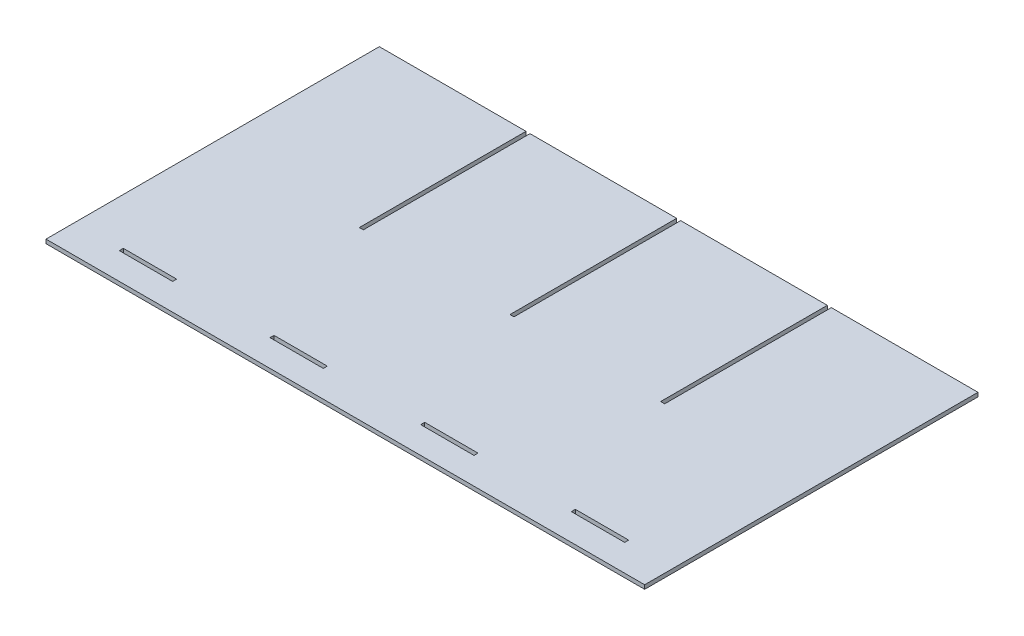
SolidWorks part; units mm, degrees
ref_plane "Front Plane" through (0, 0, 0) normal (0, 0, 1) x (1, 0, 0)
ref_plane "Top Plane" through (0, 0, 0) normal (0, 1, 0) x (1, 0, 0)
ref_plane "Right Plane" through (0, 0, 0) normal (1, 0, 0) x (0, 0, -1)
sketch "Sketch1" plane through (0, 0, 0) normal (0, 1, 0) x (1, 0, 0)
  line L0 (-162.3685, 89.9451) -> (-52.3685, 89.9451)
  line L1 (-52.3685, 89.9451) -> (-52.3685, -35.0549)
  line L2 (-49.3685, -35.0549) -> (-49.3685, 89.9451)
  line L3 (-49.3685, 89.9451) -> (60.6315, 89.9451)
  line L4 (60.6315, 89.9451) -> (60.6315, -35.0549)
  line L5 (60.6315, -35.0549) -> (63.6315, -35.0549)
  line L6 (63.6315, -35.0549) -> (63.6315, 89.9451)
  line L7 (63.6315, 89.9451) -> (173.6315, 89.9451)
  line L8 (173.6315, 89.9451) -> (173.6315, -35.0549)
  line L9 (173.6315, -35.0549) -> (176.6315, -35.0549)
  line L10 (176.6315, -35.0549) -> (176.6315, 89.9451)
  line L11 (176.6315, 89.9451) -> (286.6315, 89.9451)
  line L12 (286.6315, 89.9451) -> (286.6315, -160.0549)
  line L13 (286.6315, -160.0549) -> (-162.3685, -160.0549)
  line L14 (-162.3685, -160.0549) -> (-162.3685, 89.9451)
  line L15 (-49.3685, -35.0549) -> (-52.3685, -35.0549)
  dimension "D1" = 110
  dimension "D2" = 250
  dimension "D3" = 125
  dimension "D4" = 3
extrude "Boss-Extrude1" add sketch "Sketch1" along normal blind 3
sketch "Sketch2" plane through (0, 3, 0) normal (0, 1, 0) x (1, 0, 0)
  line L0 (-162.3685, 89.9451) -> (-162.3685, -160.0549) construction
  line L1 (-127.3685, -137.0549) -> (-87.3685, -137.0549)
  line L2 (-127.3685, -137.0549) -> (-127.3685, -140.0549)
  line L3 (-127.3685, -140.0549) -> (-87.3685, -140.0549)
  line L4 (-87.3685, -137.0549) -> (-87.3685, -140.0549)
  line L5 (-162.3685, -160.0549) -> (286.6315, -160.0549) construction
  line L6 (-14.3685, -137.0549) -> (25.6315, -137.0549)
  line L7 (-14.3685, -137.0549) -> (-14.3685, -140.0549)
  line L8 (-14.3685, -140.0549) -> (25.6315, -140.0549)
  line L9 (25.6315, -137.0549) -> (25.6315, -140.0549)
  line L10 (98.6315, -137.0549) -> (138.6315, -137.0549)
  line L11 (98.6315, -137.0549) -> (98.6315, -140.0549)
  line L12 (98.6315, -140.0549) -> (138.6315, -140.0549)
  line L13 (138.6315, -137.0549) -> (138.6315, -140.0549)
  line L14 (211.6315, -137.0549) -> (251.6315, -137.0549)
  line L15 (211.6315, -137.0549) -> (211.6315, -140.0549)
  line L16 (211.6315, -140.0549) -> (251.6315, -140.0549)
  line L17 (251.6315, -137.0549) -> (251.6315, -140.0549)
  line L18 (-52.3685, -35.0549) -> (-52.3685, 89.9451) construction
  line L19 (-49.3685, 89.9451) -> (-49.3685, -35.0549) construction
  line L20 (63.6315, 89.9451) -> (63.6315, -35.0549) construction
  line L21 (176.6315, 89.9451) -> (176.6315, -35.0549) construction
  dimension "D1" = 35
  dimension "D2" = 20
  dimension "D3" = 40
  dimension "D4" = 3
  dimension "D5" = 35
  dimension "D6" = 35
  dimension "D7" = 35
  dimension "D8" = 35
extrude "Cut-Extrude1" cut sketch "Sketch2" against normal blind 3
